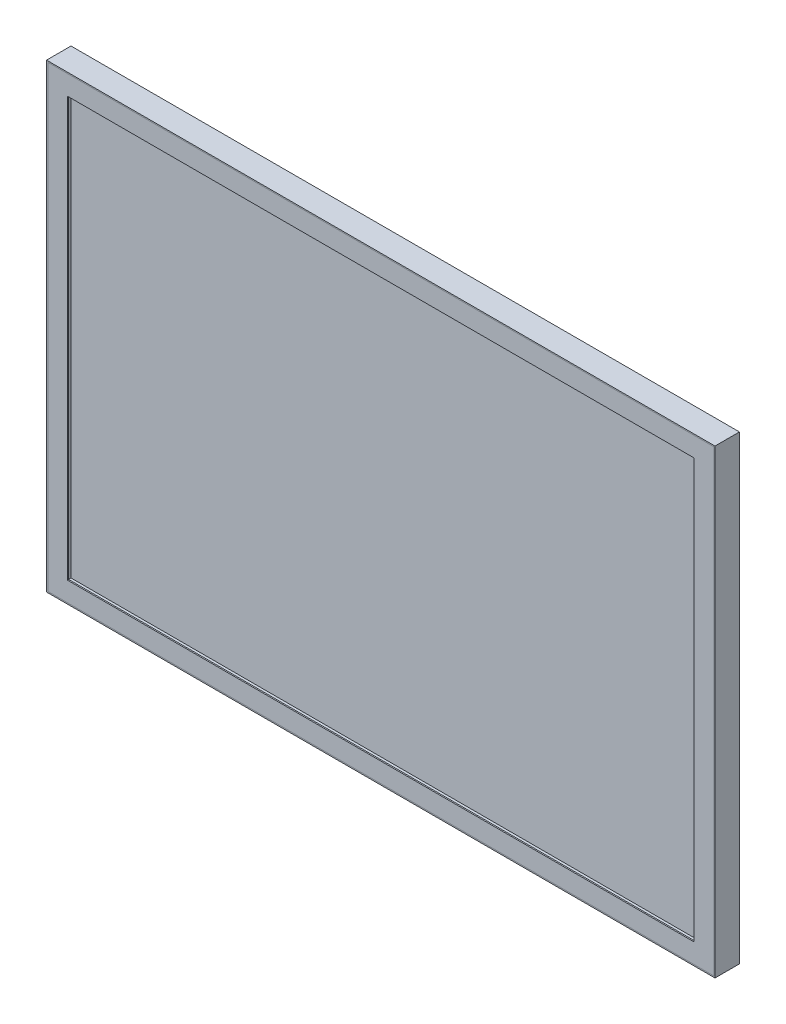
SolidWorks part; units mm, degrees
ref_plane "前视基准面" through (0, 0, 0) normal (0, 0, 1) x (1, 0, 0)
ref_plane "上视基准面" through (0, 0, 0) normal (0, 1, 0) x (1, 0, 0)
ref_plane "右视基准面" through (0, 0, 0) normal (1, 0, 0) x (0, 0, -1)
sketch "草图1" plane through (0, 0, 0) normal (0, 0, 1) x (1, 0, 0)
  line L1 (-273.5, 188.5) -> (273.5, 188.5)
  line L2 (-273.5, 188.5) -> (-273.5, -188.5)
  line L3 (-273.5, -188.5) -> (273.5, -188.5)
  line L4 (273.5, 188.5) -> (273.5, -188.5)
  line L5 (-273.5, 188.5) -> (273.5, -188.5) construction
  line L6 (-273.5, -188.5) -> (273.5, 188.5) construction
  point P0 (0, 0)
  dimension "D1" = 547
  dimension "D2" = 377
extrude "凸台-拉伸1" add sketch "草图1" along normal blind 20
shell "抽壳1" thickness 1
sketch "草图3" plane through (0, 0, 20) normal (0, 0, 1) x (1, 0, 0)
  line L0 (256.5, -171.5) -> (256.5, 171.5)
  line L1 (256.5, 171.5) -> (-256.5, 171.5)
  line L2 (-256.5, 171.5) -> (-256.5, -171.5)
  line L3 (-256.5, -171.5) -> (256.5, -171.5)
  line L4 (272.5, -187.5) -> (272.5, 187.5)
  line L5 (272.5, 187.5) -> (-272.5, 187.5)
  line L6 (-272.5, 187.5) -> (-272.5, -187.5)
  line L7 (-272.5, -187.5) -> (272.5, -187.5)
  line L8 (272.5, -187.5) -> (272.5, 187.5)
  line L9 (272.5, 187.5) -> (-272.5, 187.5)
  line L10 (-272.5, 187.5) -> (-272.5, -187.5)
  line L11 (-272.5, -187.5) -> (272.5, -187.5)
  dimension "D1" = 0
  dimension "D2" = 16
extrude "凸台-拉伸2" add sketch "草图3" against normal blind 1 separate body
